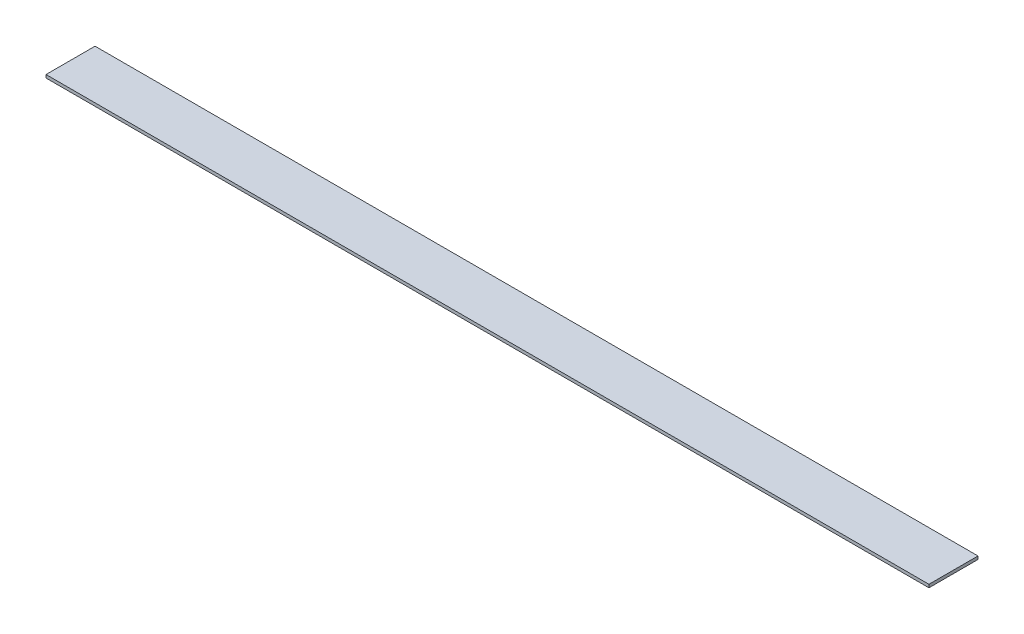
SolidWorks part; units mm, degrees
ref_plane "Front Plane" through (0, 0, 0) normal (0, 0, 1) x (1, 0, 0)
ref_plane "Top Plane" through (0, 0, 0) normal (0, 1, 0) x (1, 0, 0)
ref_plane "Right Plane" through (0, 0, 0) normal (1, 0, 0) x (0, 0, -1)
sketch "Sketch1" plane through (0, 0, 0) normal (0, 1, 0) x (1, 0, 0)
  line L1 (0, 0) -> (457.2, 0)
  line L2 (0, 0) -> (0, 25.4)
  line L3 (0, 25.4) -> (457.2, 25.4)
  line L4 (457.2, 0) -> (457.2, 25.4)
  dimension "D1" = 25.4
  dimension "D2" = 457.2
extrude "Boss-Extrude1" add sketch "Sketch1" along normal blind 1.5875
